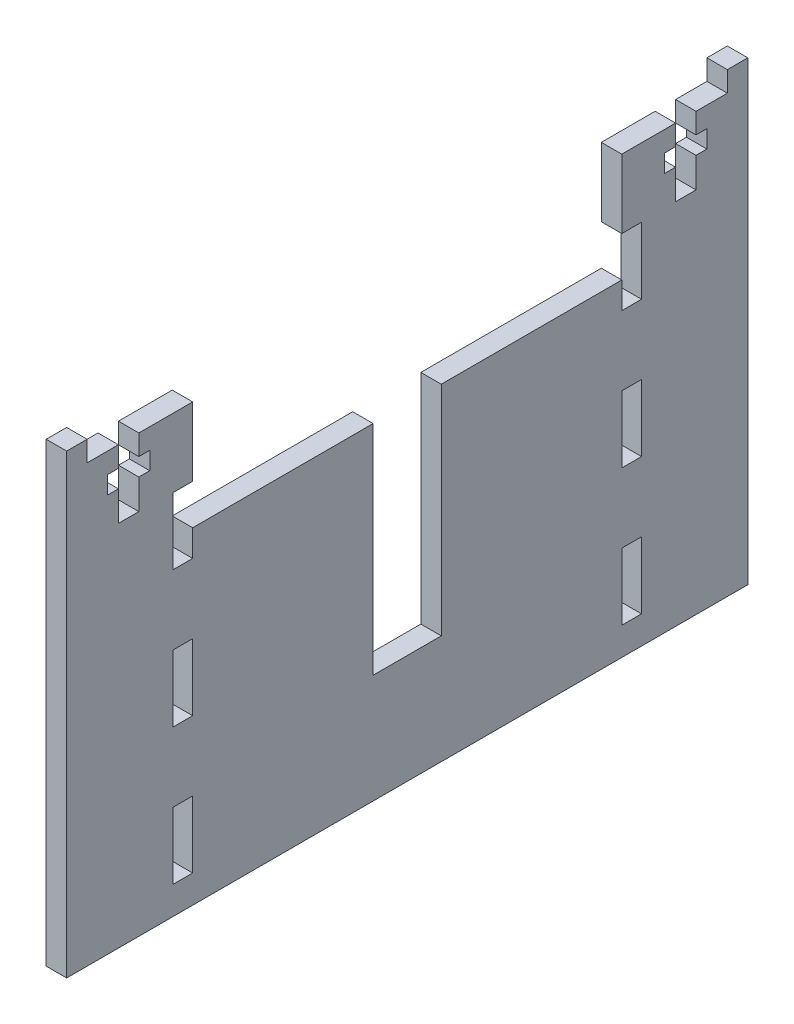
SolidWorks part; units mm, degrees
material "Acrylic (Medium-high impact)"
ref_plane "Front Plane" through (0, 0, 0) normal (0, 0, 1) x (1, 0, 0)
ref_plane "Top Plane" through (0, 0, 0) normal (0, 1, 0) x (1, 0, 0)
ref_plane "Right Plane" through (0, 0, 0) normal (1, 0, 0) x (0, 0, -1)
sketch "Sketch1" plane through (0, 0, 0) normal (1, 0, 0) x (0, 0, -1)
  line L1 (-31.5, -32) -> (31.5, -32) construction
  line L2 (-31.5, -32) -> (-31.5, 32) construction
  line L3 (-31.5, 32) -> (31.5, 32) construction
  line L4 (31.5, -32) -> (31.5, 32) construction
  line L5 (-31.5, -32) -> (31.5, 32) construction
  line L6 (-31.5, 32) -> (31.5, -32) construction
  line L7 (50, -32) -> (-50, -32)
  line L8 (50, -32) -> (50, 32)
  line L9 (50, 32) -> (-50, 32)
  line L10 (-50, -32) -> (-50, 32)
  line L11 (50, -32) -> (-50, 32) construction
  line L12 (50, 32) -> (-50, -32) construction
  point P0 (0, 0)
  point P6 (0, 0)
  dimension "D1" = 63
  dimension "D2" = 64
  dimension "D3" = 100
extrude "Boss-Extrude1" add sketch "Sketch1" along normal blind 3 contours L10 L9 L8 L7
sketch "Sketch2" plane through (3, 0, 0) normal (1, 0, 0) x (0, 0, -1)
  line L0 (31.5, -32) -> (31.5, 32) construction
  line L1 (-31.5, -32) -> (-31.5, 32) construction
  line L2 (31.5, -32) -> (31.5, 32) construction
  line L3 (-31.5, -32) -> (-31.5, 32) construction
  line L5 (-31.5, 21.9) -> (-34.4, 21.9)
  line L6 (-31.5, 21.9) -> (-31.5, 12.1)
  line L7 (-31.5, 12.1) -> (-34.4, 12.1)
  line L8 (-34.4, 21.9) -> (-34.4, 12.1)
  line L9 (50, 32) -> (-50, 32) construction
  line L10 (-31.5, 1.9) -> (-31.5, -7.9)
  line L11 (-31.5, 1.9) -> (-34.4, 1.9)
  line L12 (-34.4, 1.9) -> (-34.4, -7.9)
  line L13 (-31.5, -7.9) -> (-34.4, -7.9)
  line L14 (-31.5, -18.1) -> (-31.5, -27.9)
  line L15 (-31.5, -18.1) -> (-34.4, -18.1)
  line L16 (-34.4, -18.1) -> (-34.4, -27.9)
  line L17 (-31.5, -27.9) -> (-34.4, -27.9)
  line L18 (0, 0) -> (0, 32) construction
  line L19 (31.5, -18.1) -> (34.4, -18.1)
  line L20 (34.4, -18.1) -> (34.4, -27.9)
  line L21 (31.5, -27.9) -> (34.4, -27.9)
  line L22 (31.5, -18.1) -> (31.5, -27.9)
  line L23 (31.5, 1.9) -> (34.4, 1.9)
  line L24 (34.4, 1.9) -> (34.4, -7.9)
  line L25 (31.5, -7.9) -> (34.4, -7.9)
  line L26 (31.5, 1.9) -> (31.5, -7.9)
  line L27 (31.5, 12.1) -> (34.4, 12.1)
  line L28 (34.4, 21.9) -> (34.4, 12.1)
  line L29 (31.5, 21.9) -> (34.4, 21.9)
  line L30 (31.5, 21.9) -> (31.5, 12.1)
  dimension "D1" = 2.9
  dimension "D2" = 9.8
  dimension "D3" = 10.1
  dimension "D5" = 10.2
  dimension "D4" = 3
extrude "Cut-Extrude1" cut sketch "Sketch2" against normal blind 3
sketch "Sketch3" plane through (3, 0, 0) normal (1, 0, 0) x (0, 0, -1)
  line L0 (-31.75, 32) -> (31.75, 32) construction
  line L1 (0, 32) -> (0, 0) construction
  line L2 (50, 32) -> (-50, 32) construction
  line L3 (-42.4, 32) -> (-42.4, 29)
  line L4 (-42.4, 29) -> (-44, 29)
  line L5 (-44, 29) -> (-44, 26.4)
  line L6 (-44, 26.4) -> (-42.4, 26.4)
  line L7 (-42.4, 26.4) -> (-42.4, 22)
  line L8 (-42.4, 22) -> (-39.4, 22)
  line L9 (-42.4, 32) -> (-39.4, 32)
  line L10 (-40.9, 32) -> (-40.9, 22) construction
  line L11 (-39.4, 26.4) -> (-39.4, 22)
  line L12 (-37.8, 26.4) -> (-39.4, 26.4)
  line L13 (-37.8, 29) -> (-37.8, 26.4)
  line L14 (-39.4, 29) -> (-37.8, 29)
  line L15 (-39.4, 32) -> (-39.4, 29)
  line L16 (-34.4, 21.9) -> (-34.4, 12.1) construction
  point P9 (-40.906, 29)
  dimension "D1" = 63.5
  dimension "D2" = 10
  dimension "D3" = 3
  dimension "D4" = 1.5
  dimension "D5" = 3.1
  dimension "D6" = 5
  dimension "D7" = 2.6
extrude "Cut-Extrude2" cut sketch "Sketch3" against normal blind 10
mirror "Mirror1" about plane through (0, 0, 0) normal (0, 0, 1) of "Cut-Extrude2"
sketch "Sketch5" plane through (3, 0, 0) normal (1, 0, 0) x (0, 0, -1)
  line L0 (39.4, 32) -> (-39.4, 32) construction
  line L1 (-31.5, 16) -> (31.5, 16)
  line L2 (-31.5, 16) -> (-31.5, 32)
  line L3 (-31.5, 32) -> (31.5, 32)
  line L4 (31.5, 16) -> (31.5, 32)
  line L5 (-31.5, 16) -> (31.5, 32) construction
  line L6 (-31.5, 32) -> (31.5, 16) construction
  line L7 (-31.5, 12.1) -> (-31.5, 21.9) construction
  line L9 (31.5, 21.9) -> (31.5, 12.1) construction
  point P0 (0, 24)
  dimension "D1" = 16
extrude "Cut-Extrude3" cut sketch "Sketch5" against normal blind 10
sketch "Sketch6" plane through (3, 0, 0) normal (1, 0, 0) x (0, 0, -1)
  line L0 (-31.5, 16) -> (31.5, 16) construction
  line L1 (-5, -16) -> (5, -16)
  line L2 (-5, -16) -> (-5, 16)
  line L3 (-5, 16) -> (5, 16)
  line L4 (5, -16) -> (5, 16)
  line L5 (-5, -16) -> (5, 16) construction
  line L6 (-5, 16) -> (5, -16) construction
  point P0 (0, 0)
  dimension "D1" = 10
extrude "Cut-Extrude4" cut sketch "Sketch6" against normal blind 10
sketch "Sketch7" plane through (3, 0, 0) normal (1, 0, 0) x (0, 0, -1)
  line L0 (0, 0) -> (0, 37.1478) construction
  line L1 (-50, 32) -> (-47, 32)
  line L2 (-50, 32) -> (-50, 35)
  line L3 (-50, 35) -> (-47, 35)
  line L4 (-47, 32) -> (-47, 35)
  line L5 (47, 32) -> (47, 35)
  line L6 (50, 35) -> (47, 35)
  line L7 (50, 32) -> (50, 35)
  line L8 (50, 32) -> (47, 32)
  dimension "D1" = 3
  dimension "D2" = 3
extrude "Boss-Extrude2" add sketch "Sketch7" against normal blind 3
